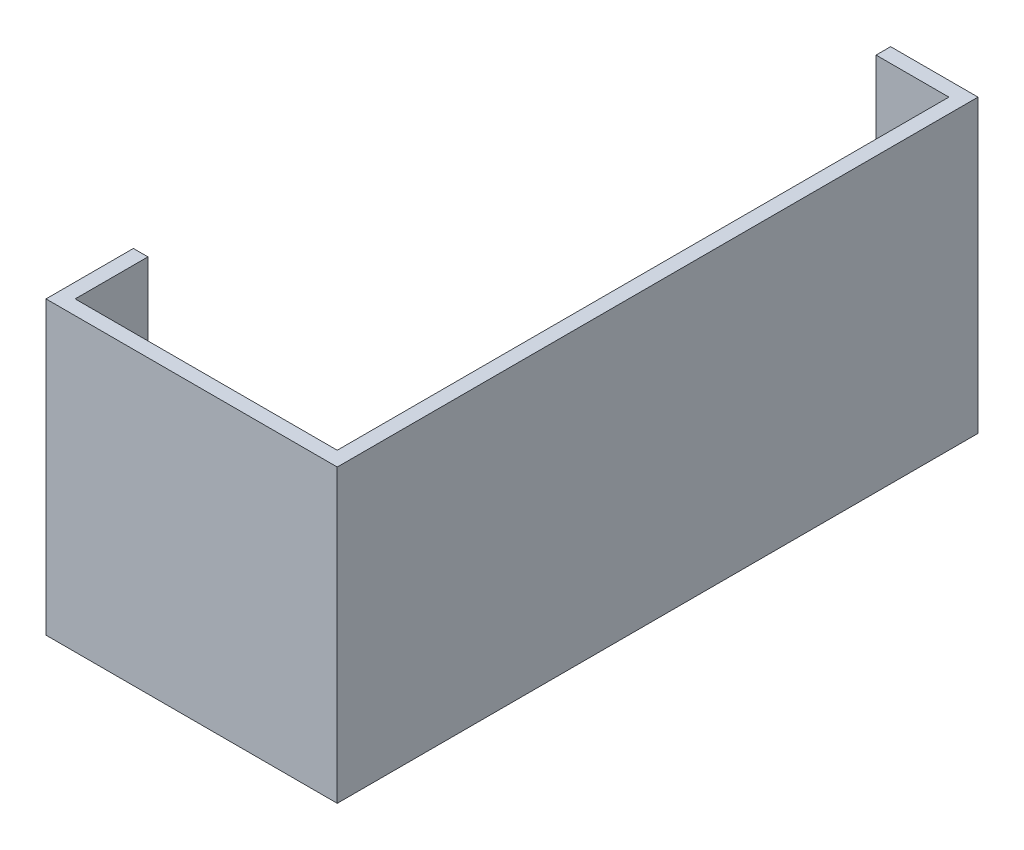
SolidWorks part; units mm, degrees
ref_plane "Piano frontale" through (0, 0, 0) normal (0, 0, 1) x (1, 0, 0)
ref_plane "Piano superiore" through (0, 0, 0) normal (0, 1, 0) x (1, 0, 0)
ref_plane "Piano destro" through (0, 0, 0) normal (1, 0, 0) x (0, 0, -1)
sketch "Schizzo1" plane through (0, 0, 0) normal (0, 1, 0) x (1, 0, 0)
  line L0 (-100, 0) -> (0, 0)
  line L1 (0, 0) -> (0, 220)
  line L2 (-100, 0) -> (-100, 30)
  line L3 (0, 220) -> (-30, 220)
  line L4 (-95, 5) -> (-95, 30)
  line L5 (-95, 5) -> (-5, 5)
  line L6 (-5, 5) -> (-5, 215)
  line L7 (-5, 215) -> (-30, 215)
  line L8 (-30, 220) -> (-30, 215)
  line L9 (-100, 30) -> (-95, 30)
  dimension "D1" = 220
  dimension "D2" = 100
  dimension "D3" = 30
  dimension "D4" = 30
  dimension "D5" = 5
extrude "Estrusione-Estrusione1" add sketch "Schizzo1" along normal blind 100
sketch "Schizzo2" plane through (0, 0, 0) normal (0, -1, 0) x (1, 0, 0)
  line L0 (-30, -215) -> (-5, -215) construction
  line L1 (-5, -215) -> (-5, -5) construction
  line L2 (-5, -5) -> (-95, -5) construction
  line L3 (-95, -5) -> (-95, -30) construction
  line L4 (-30, -215) -> (-5, -215)
  line L5 (-5, -215) -> (-5, -5)
  line L6 (-5, -5) -> (-95, -5)
  line L7 (-95, -5) -> (-95, -30)
  line L8 (-95, -30) -> (-30, -215)
extrude "Estrusione-Estrusione2" add sketch "Schizzo2" against normal blind 3
